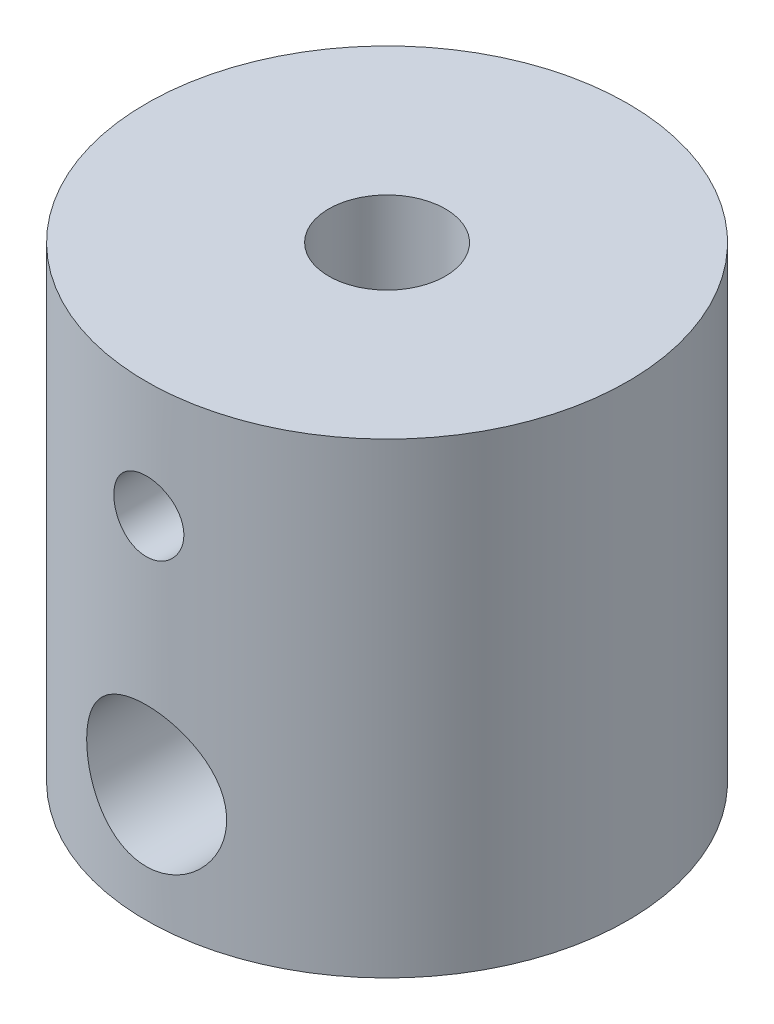
SolidWorks part; units mm, degrees
material "AISI 1045 Steel, cold drawn"
ref_plane "Front Plane" through (0, 0, 0) normal (0, 0, 1) x (1, 0, 0)
ref_plane "Top Plane" through (0, 0, 0) normal (0, 1, 0) x (1, 0, 0)
ref_plane "Right Plane" through (0, 0, 0) normal (1, 0, 0) x (0, 0, -1)
sketch "Sketch1" plane through (0, 0, 0) normal (0, 0, 1) x (1, 0, 0)
  line L0 (0, 0) -> (0, 20) construction
  line L1 (0, 20) -> (-2.5, 20) construction
  line L2 (-2.5, 20) -> (-10.3187, 20)
  line L3 (-10.3187, 20) -> (-10.3187, 0)
  line L4 (-10.3187, 0) -> (-5, 0)
  line L5 (-5, 0) -> (-5, 10)
  line L6 (-5, 10) -> (-2.5, 10)
  line L7 (-2.5, 10) -> (-2.5, 20)
  dimension "D1" = 5
  dimension "D2" = 10
  dimension "D3" = 20
  dimension "D4" = 20.6375
revolve "Revolve1" add sketch "Sketch1" angle 360 about L0
sketch "Sketch2" plane through (0, 0, 0) normal (0, 0, 1) x (1, 0, 0)
  line L0 (-10.3187, 10) -> (10.3187, 10) construction
  line L1 (-10.3187, 20) -> (-10.3187, 0) construction
  line L2 (10.3187, 0) -> (10.3187, 20) construction
  line L3 (0, 0) -> (0, 10) construction
  line L4 (0, 10) -> (0, 20) construction
  line L5 (10.3187, 20) -> (-10.3187, 20) construction
  circle A0 centre (0, 5) radius 3
  circle A1 centre (0, 15) radius 1.5
  dimension "D1" = 6
  dimension "D2" = 3
extrude "Cut-Extrude1" cut sketch "Sketch2" along normal through all
